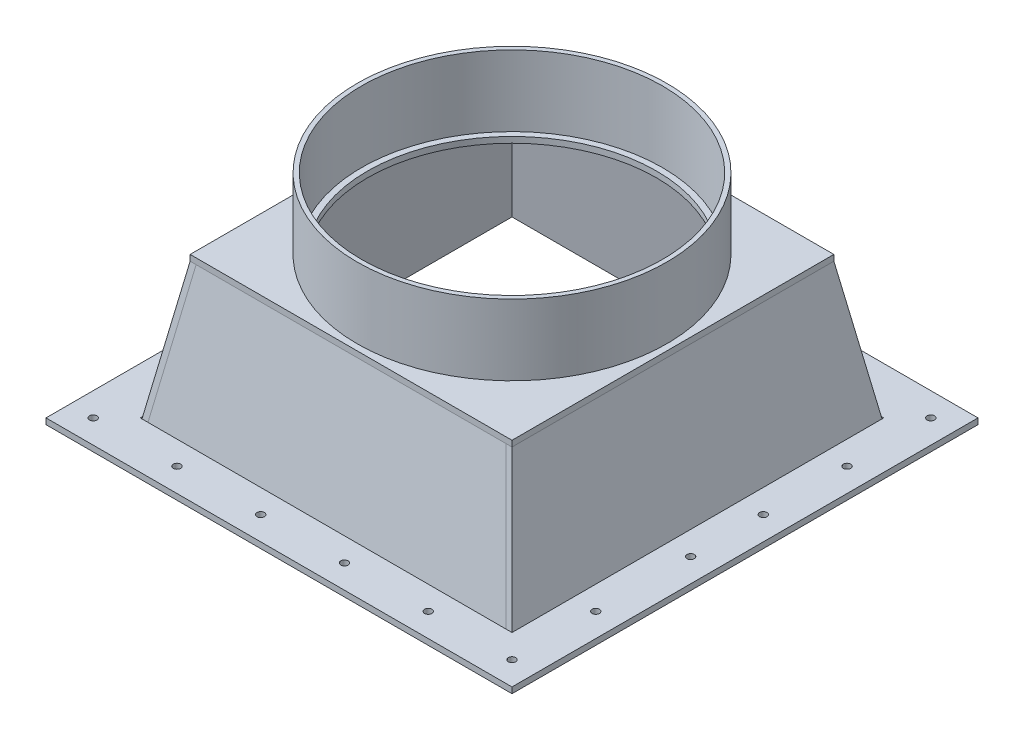
SolidWorks part; units mm, degrees
ref_plane "Front" through (0, 0, 0) normal (0, 0, 1) x (1, 0, 0)
ref_plane "Top" through (0, 0, 0) normal (0, 1, 0) x (1, 0, 0)
ref_plane "Right" through (0, 0, 0) normal (1, 0, 0) x (0, 0, -1)
sketch "Sketch8" plane through (0, 0, 0) normal (0, 0, 1) x (1, 0, 0)
  line L0 (-200.123, 0) -> (-200.123, 6.35)
  line L5 (-250.825, 0) -> (-200.123, 0)
  line L6 (-250.825, 0) -> (-250.825, 6.35)
  line L7 (-250.825, 6.35) -> (-200.123, 6.35)
  line L10 (0, 0) -> (0, 71.2164) construction
  line L13 (-200.123, 0) -> (-193.675, 0) construction
  line L14 (-200.123, 0) -> (-173.2507, 152.4)
  line L15 (-166.8028, 152.4) -> (-193.675, 0)
  line L16 (-173.2507, 152.4) -> (-173.2507, 158.75)
  line L17 (-173.2507, 158.75) -> (-166.6875, 158.75)
  line L18 (-155.575, 158.75) -> (-155.575, 152.4)
  line L19 (-155.575, 152.4) -> (-166.8028, 152.4)
  line L20 (-166.6875, 158.75) -> (-166.6875, 234.95)
  line L21 (-161.925, 158.75) -> (-161.925, 234.95)
  line L22 (-161.925, 234.95) -> (-166.6875, 234.95) construction
  line L23 (-161.925, 158.75) -> (-155.575, 158.75)
  dimension "D2" = 6.35
  dimension "D3" = 50.702
  dimension "D4" = 6.35
  dimension "D5" = 6.35
  dimension "D6" = 4.7625
  dimension "D7" = 76.2
  dimension "D8" = 323.85
  dimension "D9" = 6.35
  dimension "D10" = 100
  dimension "D11" = 152.4
  dimension "D12" = 501.65
  dimension "D13" = 387.35
  dimension "D14" = 400.2459
sketch "Sketch9" plane through (0, 0, 0) normal (0, 0, 1) x (1, 0, 0)
  line L1 (-250.825, 0) -> (250.825, 0)
  line L2 (-250.825, 0) -> (-250.825, 6.35)
  line L3 (-250.825, 6.35) -> (250.825, 6.35)
  line L4 (250.825, 0) -> (250.825, 6.35)
extrude "Boss-Extrude6" add sketch "Sketch9" along normal mid plane 501.65
sketch "Sketch10" plane through (0, 0, 0) normal (0, 0, 1) x (1, 0, 0)
  line L0 (-250.825, 0) -> (250.825, 0) construction
  line L1 (-200.123, 6.35) -> (200.123, 6.35)
  line L2 (-200.123, 6.35) -> (-200.123, 0)
  line L3 (-200.123, 0) -> (200.123, 0)
  line L4 (200.123, 6.35) -> (200.123, 0)
extrude "Cut-Extrude3" cut sketch "Sketch10" against normal mid plane 400.2459
sketch "Sketch11" plane through (0, 0, 0) normal (0, 0, 1) x (1, 0, 0)
  line L0 (-166.8028, 152.4) -> (-193.675, 0) construction
  line L1 (-200.123, 0) -> (-173.2507, 152.4) construction
  line L2 (-166.8028, 152.4) -> (-193.675, 0)
  line L3 (-200.123, 0) -> (-173.2507, 152.4)
  line L4 (-173.2507, 152.4) -> (-166.8028, 152.4)
  line L5 (-200.123, 0) -> (-193.675, 0)
extrude "Boss-Extrude8" add sketch "Sketch11" against normal up to surface and the other way up to surface separate body up to face at (0, 3.175, -200.123) other way up to face at (0, 3.175, 200.123)
mirror "Mirror1" about plane through (0, 0, 0) normal (1, 0, 0) of bodies 127
sketch "Sketch12" plane through (0, 0, 0) normal (0, 0, 1) x (1, 0, 0)
  line L1 (-173.2507, 158.75) -> (173.2507, 158.75)
  line L2 (-173.2507, 158.75) -> (-173.2507, 152.4)
  line L3 (-173.2507, 152.4) -> (173.2507, 152.4)
  line L4 (173.2507, 158.75) -> (173.2507, 152.4)
extrude "Boss-Extrude9" add sketch "Sketch12" along normal mid plane 346.5015
sketch "Sketch13" plane through (0, 0, 0) normal (1, 0, 0) x (0, 0, -1)
  line L0 (-173.2507, 152.4) -> (-200.123, 0)
  line L1 (-173.2507, 152.4) -> (-166.8028, 152.4)
  line L2 (-173.2507, 152.4) -> (173.2507, 152.4) construction
  line L3 (-166.8028, 152.4) -> (-193.675, 0)
  line L4 (-200.123, 0) -> (-193.675, 0)
  line L5 (166.8028, 152.4) -> (173.2507, 152.4)
  line L6 (173.2507, 152.4) -> (200.123, 0)
  line L7 (-250.825, 0) -> (250.825, 0) construction
  line L8 (200.123, 0) -> (200.123, 6.35) construction
  line L9 (200.123, 0) -> (193.675, 0)
  line L10 (193.675, 0) -> (166.8028, 152.4)
  line L11 (-186.6868, 76.2) -> (-180.4333, 75.0973) construction
  line L12 (186.6868, 76.2) -> (180.4333, 75.0973) construction
  dimension "D1" = 6.35
extrude "Boss-Extrude10" add sketch "Sketch13" against normal up to surface and the other way up to surface separate body up to face at (-175.7602, 101.6, 0) other way up to face at (175.7602, 101.6, 0)
sketch "Sketch14" plane through (0, 0, 0) normal (1, 0, 0) x (0, 0, -1)
  line L0 (-173.2507, 152.4) -> (-200.123, 152.4)
  line L1 (-200.123, 152.4) -> (-200.123, 0)
  line L2 (-200.123, 0) -> (-173.2507, 152.4)
  line L3 (173.2507, 152.4) -> (200.123, 0)
  line L4 (200.123, 0) -> (200.123, 152.4)
  line L5 (200.123, 152.4) -> (173.2507, 152.4)
extrude "Cut-Extrude4" cut sketch "Sketch14" against normal up to surface and the other way up to surface
sketch "Sketch15" plane through (0, 158.75, 0) normal (0, 1, 0) x (1, 0, 0)
  circle A0 centre (0, 0) radius 161.925
  circle A1 centre (0, 0) radius 166.6875
extrude "Boss-Extrude11" add sketch "Sketch15" along normal blind 76.2 separate body
sketch "Sketch16" plane through (0, 158.75, 0) normal (0, 1, 0) x (1, 0, 0)
  circle A0 centre (0, 0) radius 155.575
extrude "Cut-Extrude5" cut sketch "Sketch16" against normal through all
hole_wizard "5/16 (0.3125) Diameter Hole1" positions "Sketch17" profile "Sketch18" hole size "5/16" standard "ANSI Inch" end condition through all
sketch "Sketch17" plane through (0, 6.35, 0) normal (0, 1, 0) x (1, 0, 0)
  line L4 (-225.425, 225.425) -> (-250.825, 225.425) construction
  line L5 (-250.825, -250.825) -> (-250.825, 250.825) construction
  line L6 (-225.425, 225.425) -> (-225.425, 250.825) construction
  line L7 (250.825, 250.825) -> (-250.825, 250.825) construction
  line L8 (-225.425, -225.425) -> (-225.425, -250.825) construction
  line L9 (250.825, -250.825) -> (-250.825, -250.825) construction
  line L10 (225.425, 225.425) -> (250.825, 225.425) construction
  line L11 (250.825, -250.825) -> (250.825, 250.825) construction
  line L12 (-225.425, 225.425) -> (-225.425, 135.255) construction
  line L13 (-225.425, 135.255) -> (-225.425, 45.085) construction
  line L14 (-225.425, 45.085) -> (-225.425, -45.085) construction
  line L15 (-225.425, -45.085) -> (-225.425, -135.255) construction
  line L16 (-225.425, -135.255) -> (-225.425, -225.425) construction
  line L17 (-225.425, -225.425) -> (-135.255, -225.425) construction
  line L18 (-135.255, -225.425) -> (-45.085, -225.425) construction
  line L19 (-45.085, -225.425) -> (45.085, -225.425) construction
  line L20 (45.085, -225.425) -> (135.255, -225.425) construction
  line L21 (135.255, -225.425) -> (225.425, -225.425) construction
  point P4 (-225.425, 225.425)
  point P24 (-225.425, -225.425)
  point P26 (225.425, -225.425)
  point P28 (225.425, 225.425)
  point P51 (-225.425, 135.255)
  point P53 (-225.425, 45.085)
  point P55 (-225.425, -45.085)
  point P57 (-225.425, -135.255)
  point P59 (-135.255, -225.425)
  point P61 (-45.085, -225.425)
  point P63 (45.085, -225.425)
  point P65 (135.255, -225.425)
  point P67 (225.425, -135.255)
  point P69 (225.425, -33.1779)
  point P71 (225.425, 45.085)
  point P73 (225.425, 135.255)
  point P75 (135.255, 225.425)
  point P77 (45.085, 225.425)
  point P79 (-45.085, 225.425)
  point P81 (-135.255, 225.425)
  dimension "D1" = 25.4
  dimension "D2" = 90.17
sketch "Sketch18" plane through (-225.425, 6.35, -225.425) normal (1, 0, 0) x (0, 0, 1)
  line L0 (0, 0) -> (0, 6.35)
  line L1 (0, 6.35) -> (3.9687, 6.35)
  line L2 (3.9687, 6.35) -> (3.9688, 0)
  line L5 (3.9688, 0) -> (0, 0)
  line L11 (0, -6.35) -> (0, 107.95) construction
  dimension "Thru Hole Dia." = 7.9375
  dimension "Thru Hole Depth" = 6.35
